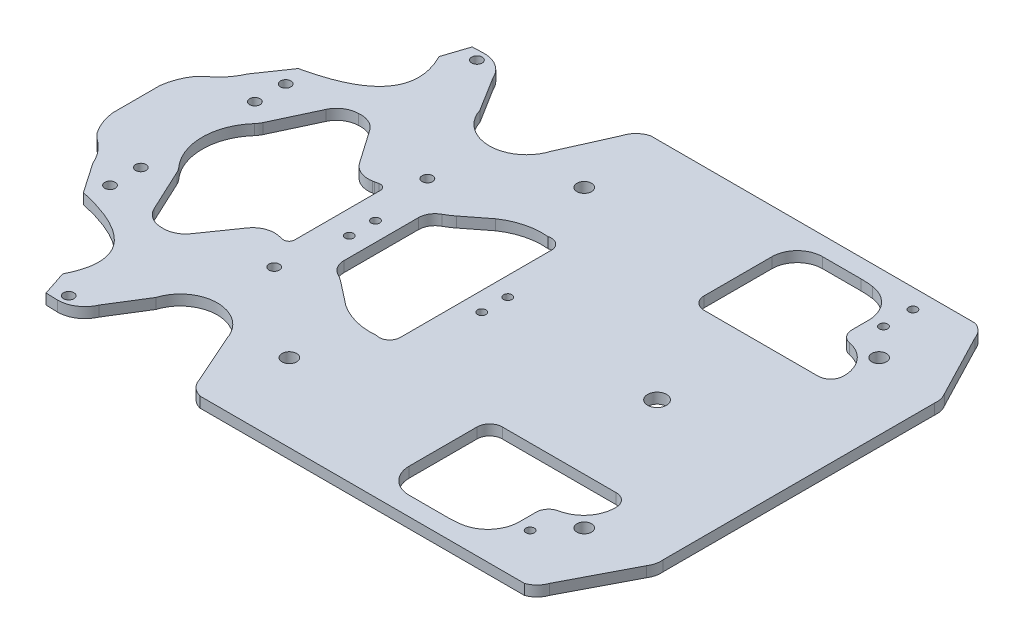
SolidWorks part; units mm, degrees
ref_plane "Front Plane" through (0, 0, 0) normal (0, 0, 1) x (1, 0, 0)
ref_plane "Top Plane" through (0, 0, 0) normal (0, 1, 0) x (1, 0, 0)
ref_plane "Right Plane" through (0, 0, 0) normal (1, 0, 0) x (0, 0, -1)
sketch "Sketch1" plane through (0, 0, 0) normal (0, 1, 0) x (1, 0, 0)
  line L0 (-1006.0615, 0) -> (49297.0144, 0) construction
  line L1 (0, -1006.0615) -> (0, 49297.0144) construction
  line L2 (22.6416, -35.6321) -> (22.6416, 36.6528)
  line L3 (-131.9469, 25.9707) -> (-134.5926, 23.325)
  line L4 (-139.1403, 11.3326) -> (-139.1403, -11.3326)
  line L14 (154.1211, 107.7645) -> (-0.9532, 107.7645)
  line L15 (-7.983, 100.9277) -> (-18.4229, 77.5008)
  line L16 (-52.3872, 77.5008) -> (-62.7788, 94.1787)
  line L17 (-74.7963, 102.0769) -> (-80.4773, 101.8961)
  line L18 (-113.129, 51.3461) -> (-122.9646, 37.0303)
  line L19 (-89.5547, 41.1174) -> (-99.1472, 20.5934)
  line L21 (-59.2972, 26.8424) -> (-71.0474, 43.7121)
  line L22 (-46.1423, 23.0747) -> (-47.8994, 22.711)
  line L23 (-42.9963, -20.5131) -> (-42.9963, 20.5133)
  line L24 (-47.8994, -22.7109) -> (-46.1423, -23.0746)
  line L25 (-70.3197, -42.6671) -> (-59.2972, -26.8423)
  line L26 (-80.0758, -47.15) -> (-78.9053, -47.15)
  line L27 (-99.1472, -20.5932) -> (-89.5547, -41.1172)
  line L28 (-14.2032, -27.1273) -> (-3.6838, -35.346)
  line L29 (-22.6416, 18.3071) -> (-22.6416, -17.2863)
  line L30 (-3.6838, 36.3667) -> (-14.2032, 28.1481)
  line L31 (144.5873, 54.2988) -> (144.5873, 54.7511)
  line L32 (84.0872, 48.2625) -> (138.5509, 48.2625)
  line L33 (78.0508, 86.7443) -> (78.0508, 54.2988)
  line L34 (108.4177, 98.8171) -> (90.1236, 98.8171)
  line L35 (127.4737, 75.4936) -> (127.4737, 83.4646)
  line L41 (160.1798, 101.7246) -> (176.0512, 71.2065)
  line L42 (177.5572, 64.9188) -> (177.5572, -64.9188)
  line L44 (-131.9469, -25.9707) -> (-134.5926, -23.325)
  line L46 (-74.7963, -102.0769) -> (-80.4773, -101.8961)
  line L47 (-52.3872, -77.5008) -> (-62.7788, -94.1787)
  line L48 (-7.983, -100.9277) -> (-18.4229, -77.5008)
  line L49 (154.1211, -107.7645) -> (-0.9532, -107.7645)
  line L50 (160.1798, -101.7246) -> (176.0512, -71.2065)
  line L51 (0, 75) -> (150, 75) construction
  line L52 (150, 75) -> (150, 0) construction
  line L53 (75, 0) -> (75, 123.0883) construction
  line L54 (84.0872, -48.2625) -> (138.5509, -48.2625)
  line L55 (78.0508, -86.7443) -> (78.0508, -54.2988)
  line L56 (108.4177, -98.8171) -> (90.1236, -98.8171)
  line L57 (127.4737, -75.4936) -> (127.4737, -83.4646)
  line L58 (144.5873, -54.2988) -> (144.5873, -54.7511)
  line L59 (-80.4773, 101.8961) -> (-84.3962, 89.9872)
  line L60 (-80.4773, -101.8961) -> (-84.3962, -89.9872)
  line L61 (-113.129, -51.3461) -> (-122.9646, -37.0303)
  line L62 (-76.9094, 97.603) -> (-70.9012, 97.603) construction
  line L63 (-73.9053, 100.6027) -> (-73.9053, 94.6033) construction
  line L64 (-109.7552, 44.9623) -> (-109.7552, 39.0259) construction
  line L65 (-112.7847, 41.9941) -> (-106.7258, 41.9941) construction
  line L66 (-113.0338, 27.2541) -> (-106.4766, 27.2541) construction
  line L67 (-109.7552, 30.327) -> (-109.7552, 24.1812) construction
  line L68 (-109.7552, -24.2848) -> (-109.7552, -30.2234) construction
  line L69 (-113.267, -27.2541) -> (-106.2434, -27.2541) construction
  line L70 (-109.7552, -41.9941) -> (-105.2674, -41.9941) construction
  line L71 (-109.7552, -39.1658) -> (-109.7552, -44.8224) construction
  line L72 (-73.9053, -97.603) -> (-73.9053, -101.4875) construction
  line L73 (-78.7712, -97.603) -> (-69.0394, -97.603) construction
  line L74 (-1.9389, -70.5) -> (10.9389, -70.5) construction
  line L75 (4.5, -64.4507) -> (4.5, -76.5493) construction
  line L76 (-36.6422, -30.6733) -> (-36.6422, -42.5871) construction
  line L77 (-43.0672, -36.6302) -> (-30.2171, -36.6302) construction
  line L78 (-34.9083, -5.6816) -> (-28.3748, -5.6816) construction
  line L79 (-31.6416, -1.6528) -> (-31.6416, -9.7105) construction
  line L80 (-31.6416, 10.4722) -> (-31.6416, 3.1243) construction
  line L81 (-35.0801, 6.7983) -> (-28.203, 6.7983) construction
  line L82 (-41.6428, 36.6302) -> (-31.6416, 36.6302) construction
  line L83 (-36.6422, 40.497) -> (-36.6422, 32.7634) construction
  line L84 (4.5, 77.1443) -> (4.5, 63.8557) construction
  line L85 (-1.9389, 70.5) -> (10.9389, 70.5) construction
  line L86 (136.8789, -70.5) -> (154.1211, -70.5) construction
  line L87 (145.5, -64.833) -> (145.5, -76.167) construction
  line L88 (133.6172, -80.9113) -> (133.6172, -88.054) construction
  line L89 (129.1568, -84.4826) -> (138.0775, -84.4826) construction
  line L90 (95.5966, -0.0984) -> (124.1593, 0) construction
  line L91 (109.878, 10.4415) -> (109.878, -10.5399) construction
  line L92 (145.5, 79.2509) -> (145.5, 61.7491) construction
  line L93 (136.3507, 70.5) -> (154.6493, 70.5) construction
  line L94 (130.8837, 84.4826) -> (136.3507, 84.4826) construction
  line L95 (133.6172, 87.3321) -> (133.6172, 81.6332) construction
  line L96 (133.6172, 101.9085) -> (133.6172, 95.1614) construction
  line L97 (129.9982, 98.535) -> (137.2361, 98.535) construction
  arc A4 (31.6416, 4.7983) -> (31.6416, 8.7983) centre (31.6416, 6.7983) ccw
  arc A5 (31.6416, 8.7983) -> (31.6416, 4.7983) centre (31.6416, 6.7983) ccw
  arc A6 (-134.5926, 23.325) -> (-139.1403, 11.3326) centre (-112.3365, 8.0266) ccw
  arc A16 (177.5572, 64.9188) -> (176.0512, 71.2065) centre (167.8533, 65.9187) ccw
  arc A17 (160.1798, 101.7246) -> (154.1211, 107.7645) centre (150.9602, 98.535) ccw
  arc A18 (-0.9532, 107.7645) -> (-7.983, 100.9277) centre (1.5137, 98.1953) ccw
  arc A20 (-62.7788, 94.1787) -> (-74.7963, 102.0769) centre (-74.7878, 88.9981) ccw
  arc A22 (-131.9469, 25.9707) -> (-122.9646, 37.0303) centre (-147.0173, 47.3877) ccw
  arc A23 (-100.8136, 18.0637) -> (-99.1472, 20.5934) centre (-108.626, 25.0236) ccw
  arc A24 (-80.1832, 47.1496) -> (-89.5547, 41.1174) centre (-80.0758, 36.6871) ccw
  arc A25 (-71.0474, 43.7121) -> (-80.1832, 47.1496) centre (-78.9053, 36.6871) ccw
  arc A26 (-59.2972, 26.8424) -> (-50.7116, 22.3595) centre (-50.7116, 32.8226) ccw
  arc A27 (-50.7116, 22.3595) -> (-48.8423, 22.5279) centre (-50.7116, 32.8226) ccw
  arc A28 (-48.8423, 22.5279) -> (-47.8994, 22.711) centre (-55.8523, 61.133) ccw
  arc A29 (-45.6121, 23.129) -> (-46.1423, 23.0747) centre (-45.6121, 20.5133) ccw
  arc A30 (-42.9963, 20.5133) -> (-45.6121, 23.129) centre (-45.6121, 20.5133) ccw
  arc A31 (-45.6121, -23.1289) -> (-42.9963, -20.5131) centre (-45.6121, -20.5131) ccw
  arc A32 (-46.1423, -23.0746) -> (-45.6121, -23.1289) centre (-45.6121, -20.5131) ccw
  arc A33 (-47.8994, -22.7109) -> (-48.8423, -22.5277) centre (-55.8523, -61.1328) ccw
  arc A34 (-48.8423, -22.5277) -> (-59.2972, -26.8423) centre (-50.7116, -32.8224) ccw
  arc A35 (-78.9053, -47.15) -> (-70.3197, -42.6671) centre (-78.9053, -36.687) ccw
  arc A36 (-89.5547, -41.1172) -> (-80.0758, -47.15) centre (-80.0758, -36.687) ccw
  arc A37 (-99.1472, -20.5932) -> (-100.8136, -18.0635) centre (-108.626, -25.0235) ccw
  arc A38 (31.6416, -7.6816) -> (31.6416, -3.6816) centre (31.6416, -5.6816) ccw
  arc A39 (16.1518, 41.4668) -> (-3.6838, 36.3667) centre (13.304, 11.4196) ccw
  arc A40 (22.6416, 36.6528) -> (16.1518, 41.4668) centre (17.6113, 36.6528) ccw
  arc A41 (17.6113, -40.6624) -> (22.6416, -35.6321) centre (17.6113, -35.6321) ccw
  arc A42 (16.1518, -40.446) -> (17.6113, -40.6624) centre (17.6113, -35.6321) ccw
  arc A43 (-3.6838, -35.346) -> (16.1518, -40.446) centre (13.304, -10.3988) ccw
  arc A44 (-14.2032, -27.1273) -> (-18.4229, -24.3652) centre (-32.785, -50.9109) ccw
  arc A45 (-22.6416, -17.2863) -> (-18.4229, -24.3652) centre (-14.5931, -17.2863) ccw
  arc A46 (-18.4229, 25.386) -> (-22.6416, 18.3071) centre (-14.5931, 18.3071) ccw
  arc A47 (-18.4229, 25.386) -> (-14.2032, 28.1481) centre (-32.785, 51.9317) ccw
  arc A48 (31.6416, -3.6816) -> (31.6416, -7.6816) centre (31.6416, -5.6816) ccw
  arc A59 (109.878, 4.4781) -> (109.878, -4.5765) centre (109.878, -0.0492) ccw
  arc A60 (109.878, -4.5765) -> (109.878, 4.4781) centre (109.878, -0.0492) ccw
  arc A65 (138.5509, 48.2625) -> (144.5873, 54.2988) centre (138.5509, 54.2988) ccw
  arc A66 (78.0508, 54.2988) -> (84.0872, 48.2625) centre (84.0872, 54.2988) ccw
  arc A67 (90.1236, 98.8171) -> (78.0508, 86.7443) centre (90.1236, 86.7443) ccw
  arc A68 (114.3653, 98.4247) -> (108.4177, 98.8171) centre (108.4177, 53.5443) ccw
  arc A69 (127.4737, 83.4646) -> (114.3653, 98.4247) centre (112.3828, 83.4646) ccw
  arc A70 (127.4737, 75.4936) -> (132.3633, 69.5672) centre (133.5101, 75.4936) ccw
  arc A71 (144.5873, 54.7511) -> (132.3633, 69.5672) centre (129.4963, 54.7511) ccw
  arc A87 (-134.5926, -23.325) -> (-139.1403, -11.3326) centre (-112.3365, -8.0266) cw
  arc A88 (-131.9469, -25.9707) -> (-122.9646, -37.0303) centre (-147.0173, -47.3877) cw
  arc A90 (-62.7788, -94.1787) -> (-74.7963, -102.0769) centre (-74.7878, -88.9981) cw
  arc A92 (-0.9532, -107.7645) -> (-7.983, -100.9277) centre (1.5137, -98.1953) cw
  arc A93 (160.1798, -101.7246) -> (154.1211, -107.7645) centre (150.9602, -98.535) cw
  arc A94 (177.5572, -64.9188) -> (176.0512, -71.2065) centre (167.8533, -65.9187) cw
  arc A97 (-31.6416, -3.6816) -> (-31.6416, -7.6816) centre (-31.6416, -5.6816) cw
  arc A98 (-31.6416, -7.6816) -> (-31.6416, -3.6816) centre (-31.6416, -5.6816) cw
  arc A99 (-31.6416, 8.7983) -> (-31.6416, 4.7983) centre (-31.6416, 6.7983) cw
  arc A100 (-31.6416, 4.7983) -> (-31.6416, 8.7983) centre (-31.6416, 6.7983) cw
  circle A101 centre (145.5, 70.5) radius 3.5
  circle A102 centre (4.5, 70.5) radius 3.5
  circle A103 centre (4.5, -70.5) radius 3.5
  circle A104 centre (145.5, -70.5) radius 3.5
  arc A105 (138.5509, -48.2625) -> (144.5873, -54.2988) centre (138.5509, -54.2988) cw
  arc A106 (78.0508, -54.2988) -> (84.0872, -48.2625) centre (84.0872, -54.2988) cw
  arc A107 (90.1236, -98.8171) -> (78.0508, -86.7443) centre (90.1236, -86.7443) cw
  arc A108 (114.3653, -98.4247) -> (108.4177, -98.8171) centre (108.4177, -53.5443) cw
  arc A109 (127.4737, -83.4646) -> (114.3653, -98.4247) centre (112.3828, -83.4646) cw
  arc A110 (127.4737, -75.4936) -> (132.3633, -69.5672) centre (133.5101, -75.4936) cw
  arc A111 (144.5873, -54.7511) -> (132.3633, -69.5672) centre (129.4963, -54.7511) cw
  arc A112 (-52.3872, -77.5008) -> (-18.4229, -77.5008) centre (-35.4051, -82.8067) cw
  arc A113 (-52.3872, 77.5008) -> (-18.4229, 77.5008) centre (-35.4051, 82.8067) ccw
  circle A115 centre (-73.9053, 97.603) radius 2.5
  circle A117 centre (-36.6422, 36.6302) radius 2.5
  circle A118 centre (-36.6422, -36.6302) radius 2.5
  circle A119 centre (-73.9053, -97.603) radius 2.5
  circle A120 centre (-109.7552, -27.2541) radius 2.5
  circle A121 centre (-109.7552, -41.9941) radius 2.5
  circle A123 centre (-109.7552, 41.9941) radius 2.5
  circle A124 centre (-109.7552, 27.2541) radius 2.5
  circle A125 centre (133.6172, -84.4826) radius 2
  circle A126 centre (133.6172, 84.4826) radius 2
  circle A127 centre (133.6172, 98.535) radius 2
  spline S0 degree 3 poles (-100.8136, 18.0637) (-110.4285, 7.2712) (-110.4285, -7.271) (-100.8136, -18.0635) knots 3.977869 3.977869 3.977869 3.977869 5.446909 5.446909 5.446909 5.446909 weights 1 0.828102 0.828102 1
  spline S1 degree 3 poles (-84.3962, 89.9872) (-74.5481, 70.6177) (-84.1257, 57.7373) (-113.129, 51.3461) knots 0.072527 0.072527 0.072527 0.072527 1 1 1 1
  spline S2 degree 3 poles (-84.3962, -89.9872) (-74.5481, -70.6177) (-84.1257, -57.7373) (-113.129, -51.3461) knots 0.072527 0.072527 0.072527 0.072527 1 1 1 1
  point P211 (-73.9053, 97.603)
  point P214 (-73.9053, 97.603)
  point P216 (-109.7552, 41.9941)
  point P220 (-109.7552, 41.9941)
  point P223 (-109.7552, 27.2541)
  point P226 (-109.7552, 27.2541)
  point P228 (-109.7552, -27.2541)
  point P232 (-109.7552, -27.2541)
  point P236 (-109.7552, -41.9941)
  point P240 (-73.9053, -97.603)
  point P243 (4.5, -70.5)
  point P246 (4.5, -70.5)
  point P248 (-36.6422, -36.6302)
  point P252 (-36.6422, -36.6302)
  point P255 (-31.6416, -5.6816)
  point P258 (-31.6416, -5.6816)
  point P261 (-31.6416, 6.7983)
  point P264 (-31.6416, 6.7983)
  point P267 (-36.6422, 36.6302)
  point P270 (-36.6422, 36.6302)
  point P272 (4.5, 70.5)
  point P276 (4.5, 70.5)
  point P279 (145.5, -70.5)
  point P282 (145.5, -70.5)
  point P284 (133.6172, -84.4826)
  point P288 (133.6172, -84.4826)
  point P290 (109.878, -0.0492)
  point P293 (109.878, -0.0492)
  point P296 (145.5, 70.5)
  point P300 (145.5, 70.5)
  point P303 (133.6172, 84.4826)
  point P306 (133.6172, 84.4826)
  point P308 (133.6172, 98.535)
  point P312 (133.6172, 98.535)
  dimension "D8" = 4.5
  dimension "D9" = 4.5
  dimension "D10" = 7
  dimension "D12" = 41.0264
  dimension "D15" = 5
  dimension "D16" = 27.2541
  dimension "D17" = 14.74
  dimension "D18" = 215.529
  dimension "D20" = 11.1265
  dimension "D2" = 6.7983
  dimension "D3" = 9
  dimension "D4" = 9
  dimension "D5" = 9
  dimension "D6" = 75
  dimension "D7" = 150
  dimension "D11" = 75
  dimension "D13" = 94.2996
  dimension "D14" = 47.15
  dimension "D19" = 4.5
  dimension "D21" = 36.6302
extrude "Boss-Extrude2" add sketch "Sketch1" along normal blind 5
ref_plane "Plane3" through (0, 15, 0) normal (0, 1, 0) x (1, 0, 0)
sketch "Sketch4" plane through (0, 15, 0) normal (0, 1, 0) x (1, 0, 0)
  line L0 (-1000, 0) -> (49000, 0) construction
  line L1 (0, -1000) -> (0, 49000) construction
  line L20 (-131.9469, 25.9707) -> (-134.5926, 23.325)
  line L21 (-139.1403, 11.3326) -> (-139.1403, -11.3326)
  line L22 (-134.5926, -23.325) -> (-131.9469, -25.9707)
  line L23 (-122.9646, -37.0303) -> (-113.129, -51.3461)
  line L24 (-84.3962, -89.9872) -> (-80.4773, -101.8961)
  line L25 (-80.4773, -101.8961) -> (-74.7963, -102.0769)
  line L26 (-62.7788, -94.1787) -> (-52.3872, -77.5008)
  line L27 (-18.4229, -77.5008) -> (-7.983, -100.9277)
  line L28 (-0.9532, -107.7645) -> (154.1211, -107.7645)
  line L29 (160.1798, -101.7246) -> (176.0512, -71.2065)
  line L30 (177.5572, -64.9188) -> (177.5572, 64.9188)
  line L31 (176.0512, 71.2065) -> (160.1798, 101.7246)
  line L32 (154.1211, 107.7645) -> (-0.9532, 107.7645)
  line L33 (-7.983, 100.9277) -> (-18.4229, 77.5008)
  line L34 (-52.3872, 77.5008) -> (-62.7788, 94.1787)
  line L35 (-74.7963, 102.0769) -> (-80.4773, 101.8961)
  line L36 (-80.4773, 101.8961) -> (-84.3962, 89.9872)
  line L37 (-113.129, 51.3461) -> (-122.9646, 37.0303)
  line L38 (-131.9469, 25.9707) -> (-134.5926, 23.325)
  line L39 (-139.1403, 11.3326) -> (-139.1403, -11.3326)
  line L40 (-134.5926, -23.325) -> (-131.9469, -25.9707)
  line L41 (-122.9646, -37.0303) -> (-113.129, -51.3461)
  line L42 (-84.3962, -89.9872) -> (-80.4773, -101.8961)
  line L43 (-80.4773, -101.8961) -> (-74.7963, -102.0769)
  line L44 (-62.7788, -94.1787) -> (-52.3872, -77.5008)
  line L45 (-18.4229, -77.5008) -> (-7.983, -100.9277)
  line L46 (-0.9532, -107.7645) -> (154.1211, -107.7645)
  line L47 (160.1798, -101.7246) -> (176.0512, -71.2065)
  line L48 (177.5572, -64.9188) -> (177.5572, 64.9188)
  line L49 (176.0512, 71.2065) -> (160.1798, 101.7246)
  line L50 (154.1211, 107.7645) -> (-0.9532, 107.7645)
  line L51 (-7.983, 100.9277) -> (-18.4229, 77.5008)
  line L52 (-52.3872, 77.5008) -> (-62.7788, 94.1787)
  line L53 (-74.7963, 102.0769) -> (-80.4773, 101.8961)
  line L54 (-80.4773, 101.8961) -> (-84.3962, 89.9872)
  line L55 (-113.129, 51.3461) -> (-122.9646, 37.0303)
  circle A1 centre (-36.6422, 36.6302) radius 2.5
  circle A2 centre (-36.6422, 36.6302) radius 2.5
  circle A3 centre (-36.6422, -36.6302) radius 2.5
  circle A4 centre (-36.6422, -36.6302) radius 2.5
  circle A5 centre (-73.9053, -97.603) radius 2.5
  circle A6 centre (-73.9053, -97.603) radius 2.5
  circle A7 centre (-73.9053, 97.603) radius 2.5
  circle A8 centre (-73.9053, 97.603) radius 2.5
  circle A9 centre (-109.7552, -27.2541) radius 2.5
  circle A10 centre (-109.7552, -27.2541) radius 2.5
  circle A11 centre (145.5, 70.5) radius 3.5
  circle A12 centre (145.5, 70.5) radius 3.5
  circle A13 centre (4.5, 70.5) radius 3.5
  circle A14 centre (4.5, 70.5) radius 3.5
  circle A15 centre (4.5, -70.5) radius 3.5
  circle A16 centre (4.5, -70.5) radius 3.5
  circle A17 centre (145.5, -70.5) radius 3.5
  circle A18 centre (145.5, -70.5) radius 3.5
  circle A19 centre (-109.7552, -41.9941) radius 2.5
  circle A20 centre (-109.7552, -41.9941) radius 2.5
  circle A21 centre (-109.7552, 41.9941) radius 2.5
  circle A22 centre (-109.7552, 41.9941) radius 2.5
  circle A23 centre (-109.7552, 27.2541) radius 2.5
  circle A24 centre (-109.7552, 27.2541) radius 2.5
  circle A25 centre (133.6172, -84.4826) radius 2
  circle A26 centre (133.6172, -84.4826) radius 2
  circle A27 centre (133.6172, 84.4826) radius 2
  circle A28 centre (133.6172, 84.4826) radius 2
  circle A29 centre (133.6172, 98.535) radius 2
  circle A30 centre (133.6172, 98.535) radius 2
  arc A44 (-131.9469, 25.9707) -> (-122.9646, 37.0303) centre (-147.0173, 47.3877) ccw
  arc A45 (-134.5926, 23.325) -> (-139.1403, 11.3326) centre (-112.3365, 8.0266) ccw
  arc A46 (-139.1403, -11.3326) -> (-134.5926, -23.325) centre (-112.3365, -8.0266) ccw
  arc A47 (-122.9646, -37.0303) -> (-131.9469, -25.9707) centre (-147.0173, -47.3877) ccw
  arc A48 (-74.7963, -102.0769) -> (-62.7788, -94.1787) centre (-74.7878, -88.9981) ccw
  arc A49 (-18.4229, -77.5008) -> (-52.3872, -77.5008) centre (-35.4051, -82.8067) ccw
  arc A50 (-7.983, -100.9277) -> (-0.9532, -107.7645) centre (1.5137, -98.1953) ccw
  arc A51 (154.1211, -107.7645) -> (160.1798, -101.7246) centre (150.9602, -98.535) ccw
  arc A52 (176.0512, -71.2065) -> (177.5572, -64.9188) centre (167.8533, -65.9187) ccw
  arc A53 (177.5572, 64.9188) -> (176.0512, 71.2065) centre (167.8533, 65.9187) ccw
  arc A54 (160.1798, 101.7246) -> (154.1211, 107.7645) centre (150.9602, 98.535) ccw
  arc A55 (-0.9532, 107.7645) -> (-7.983, 100.9277) centre (1.5137, 98.1953) ccw
  arc A56 (-52.3872, 77.5008) -> (-18.4229, 77.5008) centre (-35.4051, 82.8067) ccw
  arc A57 (-62.7788, 94.1787) -> (-74.7963, 102.0769) centre (-74.7878, 88.9981) ccw
  arc A58 (-131.9469, 25.9707) -> (-122.9646, 37.0303) centre (-147.0173, 47.3877) ccw
  arc A59 (-134.5926, 23.325) -> (-139.1403, 11.3326) centre (-112.3365, 8.0266) ccw
  arc A60 (-139.1403, -11.3326) -> (-134.5926, -23.325) centre (-112.3365, -8.0266) ccw
  arc A61 (-122.9646, -37.0303) -> (-131.9469, -25.9707) centre (-147.0173, -47.3877) ccw
  arc A62 (-74.7963, -102.0769) -> (-62.7788, -94.1787) centre (-74.7878, -88.9981) ccw
  arc A63 (-18.4229, -77.5008) -> (-52.3872, -77.5008) centre (-35.4051, -82.8067) ccw
  arc A64 (-7.983, -100.9277) -> (-0.9532, -107.7645) centre (1.5137, -98.1953) ccw
  arc A65 (154.1211, -107.7645) -> (160.1798, -101.7246) centre (150.9602, -98.535) ccw
  arc A66 (176.0512, -71.2065) -> (177.5572, -64.9188) centre (167.8533, -65.9187) ccw
  arc A67 (177.5572, 64.9188) -> (176.0512, 71.2065) centre (167.8533, 65.9187) ccw
  arc A68 (160.1798, 101.7246) -> (154.1211, 107.7645) centre (150.9602, 98.535) ccw
  arc A69 (-0.9532, 107.7645) -> (-7.983, 100.9277) centre (1.5137, 98.1953) ccw
  arc A70 (-52.3872, 77.5008) -> (-18.4229, 77.5008) centre (-35.4051, 82.8067) ccw
  arc A71 (-62.7788, 94.1787) -> (-74.7963, 102.0769) centre (-74.7878, 88.9981) ccw
  parabola Q2 (-113.129, -51.3461) -> (-84.3962, -89.9872) focus (-89.6322, -73.5087) apex (-81.5532, -70.81)
  parabola Q3 (-84.3962, 89.9872) -> (-113.129, 51.3461) focus (-89.6322, 73.5087) apex (-81.5532, 70.81)
  parabola Q4 (-113.129, -51.3461) -> (-84.3962, -89.9872) focus (-89.6322, -73.5087) apex (-81.5532, -70.81)
  parabola Q5 (-84.3962, 89.9872) -> (-113.129, 51.3461) focus (-89.6322, 73.5087) apex (-81.5532, 70.81)
  dimension "D1" = 0
  dimension "D2" = 0
  dimension "D3" = 0
  dimension "D4" = 0
  dimension "D5" = 0
  dimension "D6" = 0
  dimension "D7" = 0
  dimension "D8" = 0
  dimension "D9" = 0
  dimension "D10" = 0
  dimension "D11" = 0
  dimension "D12" = 0
  dimension "D13" = 0
  dimension "D14" = 0
  dimension "D15" = 0
  dimension "D16" = 0
